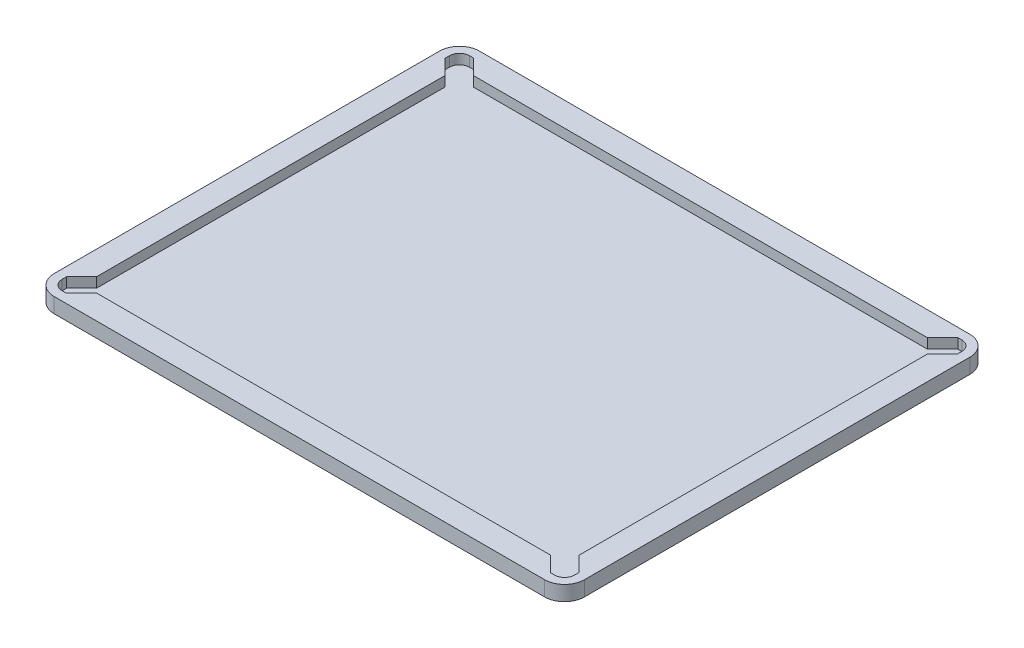
SolidWorks part; units mm, degrees
ref_plane "Front Plane" through (0, 0, 0) normal (0, 0, 1) x (1, 0, 0)
ref_plane "Top Plane" through (0, 0, 0) normal (0, 1, 0) x (1, 0, 0)
ref_plane "Right Plane" through (0, 0, 0) normal (1, 0, 0) x (0, 0, -1)
sketch "Sketch1" plane through (0, 0, 0) normal (0, 1, 0) x (1, 0, 0)
  line L1 (0, 0) -> (266, 0)
  line L2 (0, 0) -> (0, 213.3)
  line L3 (0, 213.3) -> (266, 213.3)
  line L4 (266, 0) -> (266, 213.3)
  dimension "D1" = 213.3
  dimension "D2" = 266
extrude "Boss-Extrude1" add sketch "Sketch1" along normal blind 7.5
sketch "Sketch2" plane through (0, 7.5, 0) normal (0, 1, 0) x (1, 0, 0)
  line L0 (133, 213.3) -> (133, 224.1695) construction
  line L1 (12, 201.15) -> (254, 201.15)
  line L2 (12, 201.15) -> (12, 12.15)
  line L3 (12, 12.15) -> (254, 12.15)
  line L4 (254, 201.15) -> (254, 12.15)
  line L5 (266, 213.3) -> (0, 213.3) construction
  line L6 (0, 106.65) -> (-10.1514, 106.65) construction
  line L7 (0, 213.3) -> (0, 0) construction
  dimension "D1" = 242
  dimension "D2" = 189
extrude "Cut-Extrude1" cut sketch "Sketch2" against normal blind 5
sketch "Sketch3" plane through (0, 7.5, 0) normal (0, 1, 0) x (1, 0, 0)
  line L0 (12, 194.0789) -> (4.5, 201.5789)
  line L1 (12, 201.15) -> (12, 12.15) construction
  line L2 (4.5, 201.5789) -> (4.5, 208.8)
  line L3 (4.5, 208.8) -> (11.4211, 208.8)
  line L4 (11.4211, 208.8) -> (19.0711, 201.15)
  line L5 (254, 201.15) -> (12, 201.15) construction
  line L6 (19.0711, 201.15) -> (12, 194.0789)
  line L7 (0, 213.3) -> (0, 0) construction
  line L8 (266, 213.3) -> (0, 213.3) construction
  line L9 (133, 213.3) -> (133, 230.3621) construction
  line L10 (0, 106.65) -> (-21.5582, 106.65) construction
  line L11 (19.0711, 12.15) -> (12, 19.2211)
  line L12 (11.4211, 4.5) -> (19.0711, 12.15)
  line L13 (4.5, 4.5) -> (11.4211, 4.5)
  line L14 (4.5, 11.7211) -> (4.5, 4.5)
  line L15 (12, 19.2211) -> (4.5, 11.7211)
  line L16 (266, 106.65) -> (287.5582, 106.65) construction
  line L17 (254, 19.2211) -> (261.5, 11.7211)
  line L18 (261.5, 11.7211) -> (261.5, 4.5)
  line L19 (261.5, 4.5) -> (254.5789, 4.5)
  line L20 (254.5789, 4.5) -> (246.9289, 12.15)
  line L21 (246.9289, 12.15) -> (254, 19.2211)
  line L22 (246.9289, 201.15) -> (254, 194.0789)
  line L23 (254.5789, 208.8) -> (246.9289, 201.15)
  line L24 (261.5, 208.8) -> (254.5789, 208.8)
  line L25 (261.5, 201.5789) -> (261.5, 208.8)
  line L26 (254, 194.0789) -> (261.5, 201.5789)
  dimension "D1" = 4.5
  dimension "D2" = 4.5
  dimension "D3" = 45
  dimension "D4" = 45
  dimension "D5" = 10
extrude "Cut-Extrude2" cut sketch "Sketch3" against normal blind 5
fillet "Fillet1" radius 5 4 edges at (4.5, 5, -4.5) (261.5, 5, -4.5) (261.5, 5, -208.8) (4.5, 5, -208.8)
fillet "Fillet2" radius 10 4 edges at (266, 3.75, -213.3) (266, 3.75, 0) (0, 3.75, 0) (0, 3.75, -213.3)
